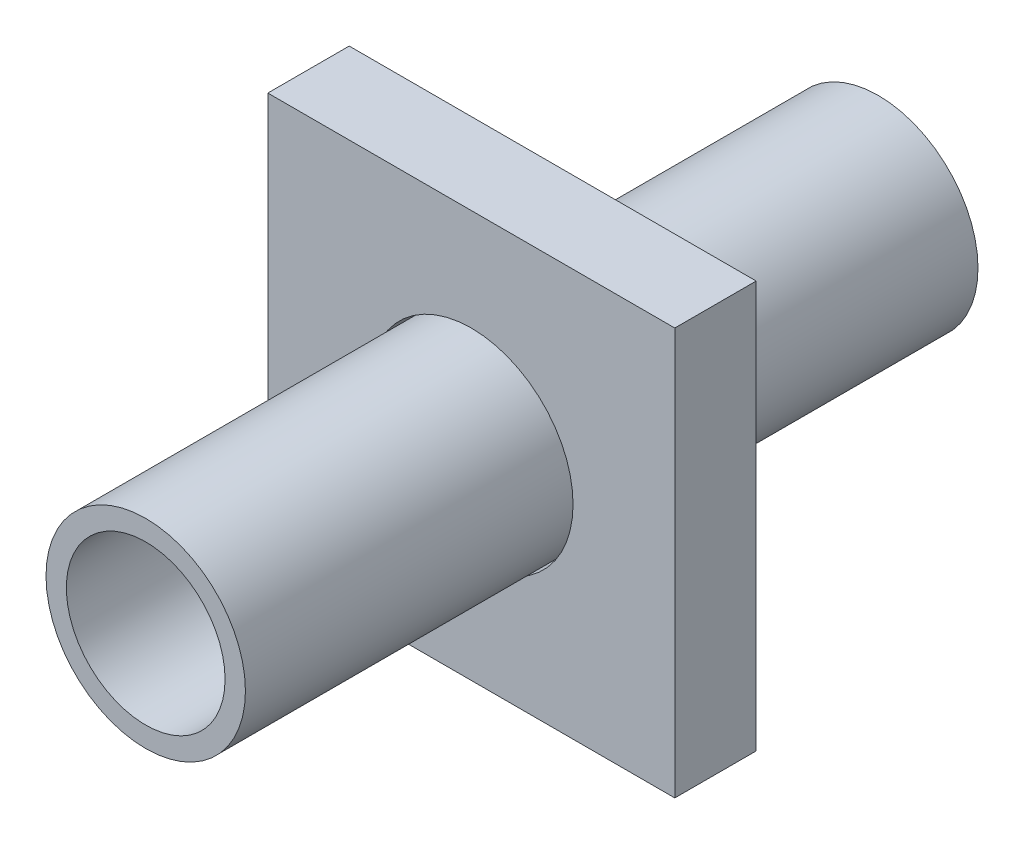
SolidWorks part; units mm, degrees
ref_plane "Front Plane" through (0, 0, 0) normal (0, 0, 1) x (1, 0, 0)
ref_plane "Top Plane" through (0, 0, 0) normal (0, 1, 0) x (1, 0, 0)
ref_plane "Right Plane" through (0, 0, 0) normal (1, 0, 0) x (0, 0, -1)
sketch "Sketch1" plane through (0, 0, 0) normal (0, 0, 1) x (1, 0, 0)
  line L1 (-500, 500) -> (500, 500)
  line L2 (-500, 500) -> (-500, -500)
  line L3 (-500, -500) -> (500, -500)
  line L4 (500, 500) -> (500, -500)
  line L5 (-500, 500) -> (500, -500) construction
  line L6 (-500, -500) -> (500, 500) construction
  circle A0 centre (0, 0) radius 250
  point P0 (0, 0)
  dimension "D3" = 500
  dimension "D1" = 1000
  dimension "D2" = 1000
extrude "Boss-Extrude1" add sketch "Sketch1" along normal blind 200
sketch "Sketch2" plane through (0, 0, 0) normal (0, 0, 1) x (1, 0, 0)
  circle A0 centre (0, 0) radius 245
  dimension "D1" = 490
extrude "Extrude-Thin1" add sketch "Sketch2" along normal blind 1000 and the other way blind 800 thin thin type one direction reverse wall 50
